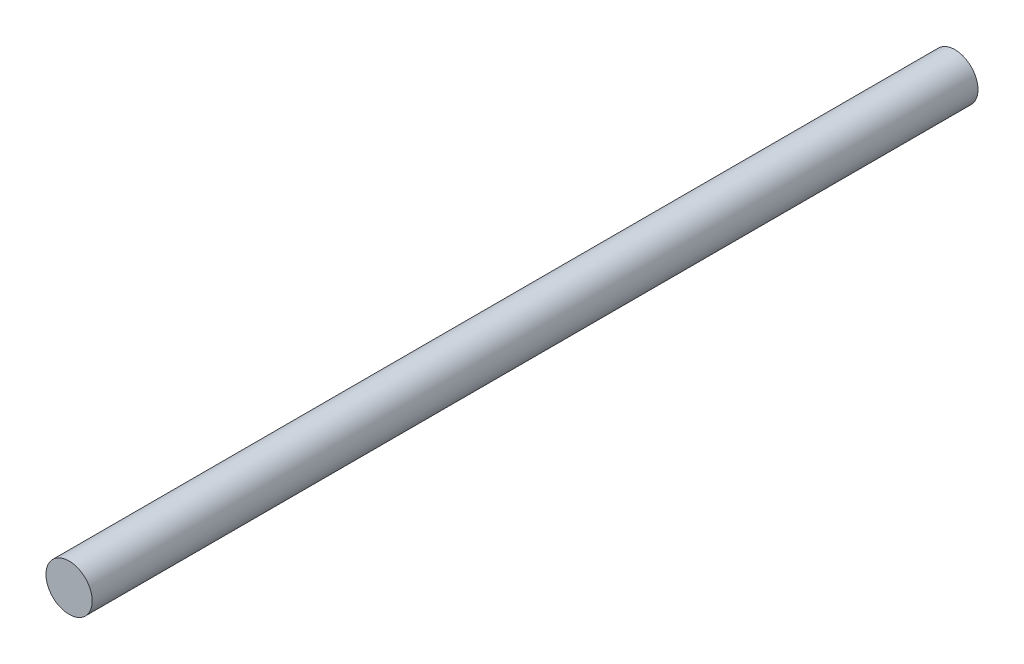
SolidWorks part; units mm, degrees
ref_plane "Front Plane" through (0, 0, 0) normal (0, 0, 1) x (1, 0, 0)
ref_plane "Top Plane" through (0, 0, 0) normal (0, 1, 0) x (1, 0, 0)
ref_plane "Right Plane" through (0, 0, 0) normal (1, 0, 0) x (0, 0, -1)
surface "Surface-Offset1" parameters "D1"=0
ref_plane "Plane1" through (0, 0, 106.365) normal (0, 0, 1) x (1, 0, 0)
ref_plane "Plane2" through (0, 0, -15.24) normal (0, 0, 1) x (1, 0, 0)
sketch "Sketch2" plane through (0, 0, 106.365) normal (0, 0, 1) x (1, 0, 0)
  circle A0 centre (-26.924, 0) radius 3.175 construction
  circle A1 centre (-26.924, 0) radius 3.175
extrude "Boss-Extrude1" add sketch "Sketch2" against normal up to surface (121.605 mm away) up to plane "Plane2"
